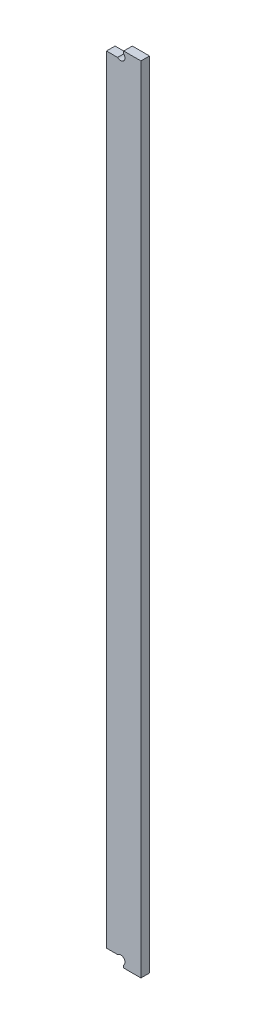
SolidWorks part; units mm, degrees
material "6061-T6 (SS)"
ref_plane "Front Plane" through (0, 0, 0) normal (0, 0, 1) x (1, 0, 0)
ref_plane "Top Plane" through (0, 0, 0) normal (0, 1, 0) x (1, 0, 0)
ref_plane "Right Plane" through (0, 0, 0) normal (1, 0, 0) x (0, 0, -1)
sketch "Sketch2" plane through (0, 0, 0) normal (0, 0, 1) x (1, 0, 0)
  line L0 (-79.025, 289.475) -> (0, 289.475) construction
  line L1 (0, 0) -> (0, 289.475) construction
  line L2 (0, 0) -> (-79.025, 0) construction
  line L3 (-79.025, 289.475) -> (0, 289.475) construction
  line L4 (0, 0) -> (0, 289.475) construction
  line L5 (0, 0) -> (-79.025, 0) construction
  line L6 (39.6875, 291.0625) -> (33.3375, 291.0625)
  line L7 (33.3375, 291.0625) -> (33.3375, 287.8875)
  line L8 (33.3375, 287.8875) -> (26.9875, 287.8875)
  line L9 (26.9875, 287.8875) -> (26.9875, 1.5875)
  line L10 (26.9875, 144.7375) -> (39.6875, 144.7375) construction
  line L11 (39.6875, -1.5875) -> (39.6875, 291.0625)
  line L12 (33.3375, 291.0625) -> (33.3375, 287.8875) construction
  line L13 (33.3375, 1.5875) -> (26.9875, 1.5875)
  line L14 (33.3375, -1.5875) -> (33.3375, 1.5875)
  line L15 (39.6875, -1.5875) -> (33.3375, -1.5875)
  line L16 (25.4, 289.475) -> (25.4, 0) construction
  line L17 (25.4, 289.475) -> (25.4, 0) construction
  point P10 (0, 144.7375)
  dimension "D3" = 1.5875
  dimension "D1" = 1.5875
  dimension "D4" = 12.7
  dimension "D2" = 1.5875
extrude "Boss-Extrude1" add sketch "Sketch2" along normal blind 3.175
sketch "Sketch3" plane through (0, 0, 0) normal (0, 0, -1) x (-1, 0, 0)
  line L0 (-39.6875, 144.7375) -> (-26.9875, 144.7375) construction
  line L2 (-33.3375, 287.8875) -> (-32.215, 287.8875) construction
  line L3 (-33.3375, 287.8875) -> (-33.3375, 289.01) construction
  line L4 (-33.3375, 289.01) -> (-32.215, 289.01) construction
  line L5 (-32.215, 287.8875) -> (-32.215, 289.01) construction
  line L8 (-39.6875, 291.0625) -> (-39.6875, -1.5875)
  line L9 (-39.6875, -1.5875) -> (-33.3375, -1.5875)
  line L10 (-33.3375, -1.5875) -> (-33.3375, 1.5875)
  line L11 (-33.3375, 1.5875) -> (-26.9875, 1.5875)
  line L12 (-26.9875, 1.5875) -> (-26.9875, 287.8875)
  line L13 (-26.9875, 287.8875) -> (-33.3375, 287.8875)
  line L14 (-33.3375, 287.8875) -> (-33.3375, 291.0625)
  line L15 (-33.3375, 291.0625) -> (-39.6875, 291.0625)
  line L16 (-39.6875, 291.0625) -> (-39.6875, -1.5875) construction
  line L17 (-39.6875, -1.5875) -> (-33.3375, -1.5875) construction
  line L18 (-33.3375, -1.5875) -> (-33.3375, 1.5875) construction
  line L19 (-33.3375, 1.5875) -> (-26.9875, 1.5875) construction
  line L20 (-26.9875, 1.5875) -> (-26.9875, 287.8875) construction
  line L21 (-26.9875, 287.8875) -> (-33.3375, 287.8875) construction
  line L22 (-33.3375, 287.8875) -> (-33.3375, 291.0625) construction
  line L23 (-33.3375, 291.0625) -> (-39.6875, 291.0625) construction
  circle A0 centre (-32.215, 289.01) radius 1.5875
  circle A1 centre (-32.215, 0.465) radius 1.5875
  dimension "D2" = 3.175
extrude "Cut-Extrude1" cut sketch "Sketch3" against normal up to surface (3.175 mm away) up to face at (33.3375, 144.7375, 3.175)
equation "\"D1@Sketch2\"=\"acc rear wall thickness@FS2-EN-ACC-A-0003-V1, ACCUMULATOR CONTAINER.Assembly\"/2"
equation "\"D3@Sketch2\"=\"acc rear wall thickness@FS2-EN-ACC-A-0003-V1, ACCUMULATOR CONTAINER.Assembly\"/2"
equation "\"D4@Sketch2\"=\"Acc Lid Flange Width@FS2-EN-ACC-A-0003-V1, ACCUMULATOR CONTAINER.Assembly\""
equation "\"D1@Boss-Extrude1\"=\"acc lid flange thickness@FS2-EN-ACC-A-0003-V1, ACCUMULATOR CONTAINER.Assembly\""
equation "\"D2@Sketch3\"=\"weld teardrop radius@FS2-EN-ACC-A-0003-V1, ACCUMULATOR CONTAINER.Assembly\"*2"
equation "\"D2@Sketch2\"=\"acc side wall thickness@FS2-EN-ACC-A-0003-V1, ACCUMULATOR CONTAINER.Assembly\"/2"
